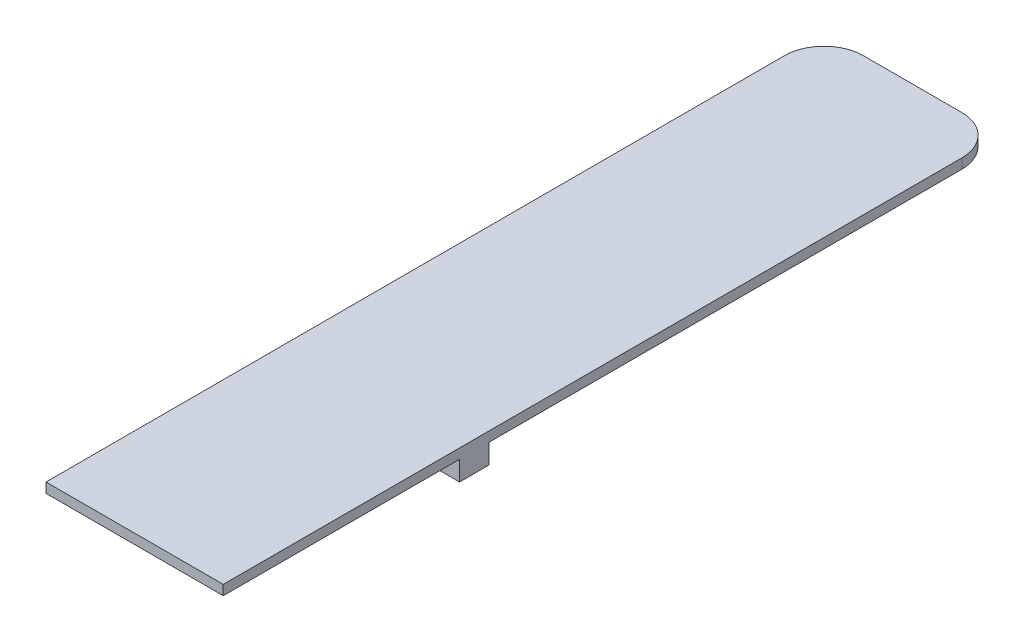
SolidWorks part; units mm, degrees
ref_plane "Front Plane" through (0, 0, 0) normal (0, 0, 1) x (1, 0, 0)
ref_plane "Top Plane" through (0, 0, 0) normal (0, 1, 0) x (1, 0, 0)
ref_plane "Right Plane" through (0, 0, 0) normal (1, 0, 0) x (0, 0, -1)
sketch "Sketch1" plane through (0, 0, 0) normal (0, 1, 0) x (1, 0, 0)
  line L11 (0, -55) -> (18, -55)
  line L18 (0, 0) -> (0, -55)
  line L19 (18, 0) -> (18, -55)
  line L26 (18, 0) -> (0, 0)
  dimension "D1" = 18
  dimension "D2" = 55
extrude "Boss-Extrude1" add sketch "Sketch1" along normal blind 1
sketch "Sketch2" plane through (0, 0, 0) normal (0, -1, 0) x (1, 0, 0)
  line L0 (18, 55) -> (18, 0) construction
  line L1 (0, 55) -> (18, 55)
  line L2 (0, 55) -> (0, 52)
  line L3 (0, 52) -> (18, 52)
  line L4 (18, 55) -> (18, 52)
  dimension "D1" = 3
extrude "Boss-Extrude2" add sketch "Sketch2" along normal blind 2
sketch "Sketch3" plane through (0, 0, 55) normal (0, 0, 1) x (1, 0, 0)
  line L4 (0, 0) -> (18, 0)
  line L5 (0, 1) -> (0, 0)
  line L6 (18, 1) -> (0, 1)
  line L7 (18, 0) -> (18, 1)
  line L8 (0, 0) -> (18, 0)
  line L9 (0, 1) -> (0, 0)
  line L10 (18, 1) -> (0, 1)
  line L11 (18, 0) -> (18, 1)
  dimension "D1" = 0
extrude "Boss-Extrude3" add sketch "Sketch3" along normal blind 24
sketch "Sketch4" plane through (0, 0, 0) normal (0, -1, 0) x (1, 0, 0)
  line L0 (9, 0) -> (9, 6) construction
  line L1 (18, 0) -> (0, 0) construction
  line L3 (5.5, 5) -> (12.5, 5)
  line L4 (5.5, 5) -> (5.5, 7)
  line L5 (5.5, 7) -> (12.5, 7)
  line L6 (12.5, 5) -> (12.5, 7)
  line L7 (5.5, 5) -> (12.5, 7) construction
  line L8 (5.5, 7) -> (12.5, 5) construction
  point P8 (9, 6.1743)
  dimension "D1" = 2
  dimension "D2" = 7
  dimension "D3" = 5
extrude "Boss-Extrude4" add sketch "Sketch4" along normal blind 2
fillet "Fillet1" radius 4 2 edges at (0, 0.5, 0) (18, 0.5, 0)
sketch "Sketch5" plane through (5.5, 0, 0) normal (-1, 0, 0) x (0, 0, 1)
  line L0 (7, 0) -> (7.6158, -2)
  line L1 (7.6158, -2) -> (7, -2)
  line L2 (7, -2) -> (7, 0)
  line L3 (5, 0) -> (5, -2)
  line L4 (5, -2) -> (4.3842, 0)
  line L5 (4.3842, 0) -> (5, 0)
  line L6 (7, -2) -> (5, -2) construction
  line L7 (7, -2) -> (7, 0) construction
  point P12 (7.5308, -2)
  point P13 (7, 0)
  point P14 (6.522, -2)
  point P15 (6, -2)
  point P18 (6, 1.0187)
  point P19 (7.998, -2)
  point P20 (6.9459, -2)
  point P21 (6, 0)
  point P23 (6.4397, -2)
  dimension "D1" = 2.5
extrude "Boss-Extrude5" add sketch "Sketch5" against normal up to surface (7 mm away) up to face at (12.5, -1, 6)
